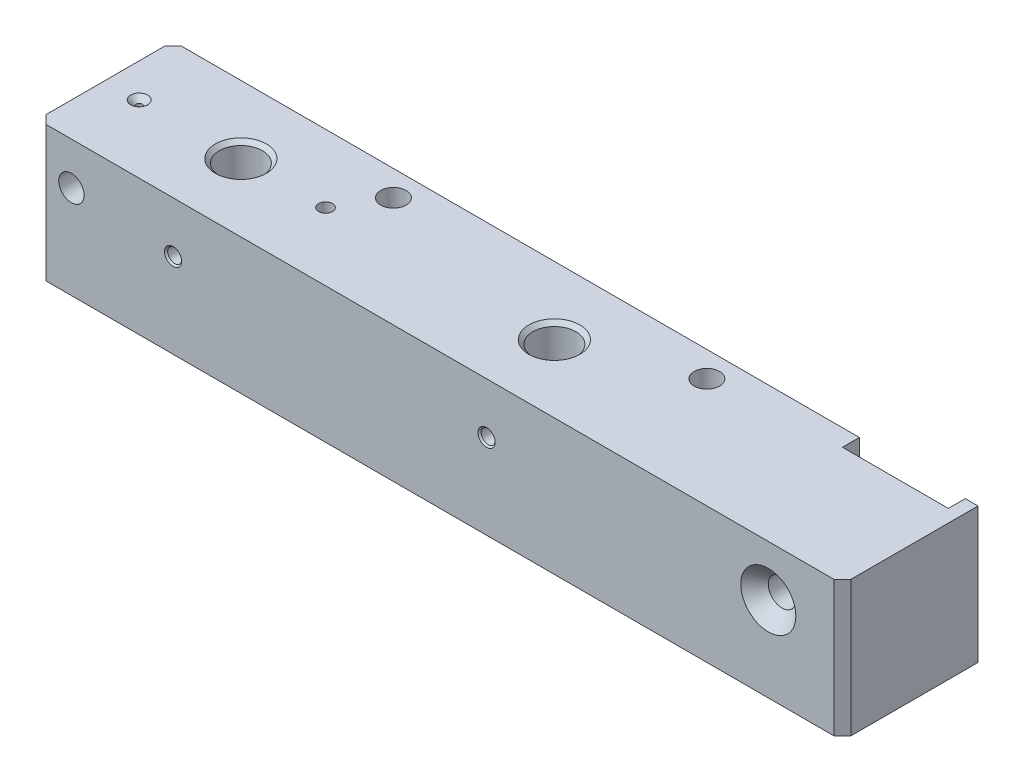
SolidWorks part; units mm, degrees
ref_plane "Front Plane" through (0, 0, 0) normal (0, 0, 1) x (1, 0, 0)
ref_plane "Top Plane" through (0, 0, 0) normal (0, 1, 0) x (1, 0, 0)
ref_plane "Right Plane" through (0, 0, 0) normal (1, 0, 0) x (0, 0, -1)
sketch "Sketch1" plane through (0, 0, 0) normal (0, 0, 1) x (1, 0, 0)
  line L1 (-95, 16) -> (95, 16)
  line L2 (-95, 16) -> (-95, -16)
  line L3 (-95, -16) -> (95, -16)
  line L4 (95, 16) -> (95, -16)
  line L5 (-95, 16) -> (95, -16) construction
  line L6 (-95, -16) -> (95, 16) construction
  point P0 (0, 0)
  dimension "D1" = 190
  dimension "D2" = 32
extrude "Boss-Extrude1" add sketch "Sketch1" along normal mid plane 32
chamfer "Chamfer1" distance 2 angle 45 3 edges at (-95, 0, -16) (-95, 0, 16) (95, 0, 16)
sketch "Sketch2" plane through (0, 16, 0) normal (0, 1, 0) x (1, 0, 0)
  line L0 (95, 16) -> (-93, 16) construction
  line L1 (67, 16) -> (92, 16)
  line L2 (67, 16) -> (67, 12)
  line L3 (67, 12) -> (92, 12)
  line L4 (92, 16) -> (92, 12)
  line L5 (95, -14) -> (95, 16) construction
  dimension "D1" = 25
  dimension "D2" = 4
  dimension "D3" = 3
extrude "Cut-Extrude1" cut sketch "Sketch2" against normal through all
sketch "Sketch3" plane through (0, 16, 0) normal (0, 1, 0) x (1, 0, 0)
  line L0 (-95, 0) -> (95, 0) construction
  line L1 (-95, -14) -> (-95, 14) construction
  line L2 (95, -14) -> (95, 16) construction
  line L3 (-63, 16) -> (-63, -16) construction
  line L4 (67, 16) -> (-93, 16) construction
  line L5 (93, -16) -> (-93, -16) construction
  line L6 (11, 16) -> (11, -16) construction
  line L7 (67, 16) -> (67, 12) construction
  dimension "D1" = 56
  dimension "D2" = 74
hole_wizard "M12 Tapped Hole1" positions "Sketch4" profile "Sketch5" tap size "M12" standard "ISO"
sketch "Sketch4" plane through (0, 16, 0) normal (0, 1, 0) x (1, 0, 0)
  line L0 (-63, 16) -> (-63, -16) construction
  line L1 (11, 16) -> (11, -16) construction
  point P0 (-63, 0)
  point P4 (11, 0)
sketch "Sketch5" plane through (-63, 16, 0) normal (1, 0, 0) x (0, 0, 1)
  line L0 (0, 0) -> (0, 27.0644)
  line L1 (0, 27.0644) -> (5.1, 24)
  line L2 (5.1, 24) -> (5.1, 0.925)
  line L3 (5.1, 0.925) -> (6.025, 0)
  line L5 (6.025, 0) -> (0, 0)
  line L6 (-5.1, 0.925) -> (-6.025, 0) construction
  line L10 (0, 27.0644) -> (-5.1, 24) construction
  line L11 (0, -6.35) -> (0, 107.95) construction
  dimension "Tap Drill Dia." = 10.2
  dimension "Tap Drill Depth" = 24
  dimension "Near C'Sink Dia." = 12.05
  dimension "Near C'Sink Angle" = 90
  dimension "Drill Angle" = 118
cosmetic thread "Hole Thread1" parameters "D1"=24, "D2"=12
cosmetic thread "Hole Thread2" parameters "D1"=24, "D2"=12
sketch "Sketch6" plane through (0, 0, 16) normal (0, 0, 1) x (1, 0, 0)
  line L0 (-63, -8) -> (-63, 16) construction
  line L1 (-57.9, -8) -> (-68.1, -8) construction
  line L2 (-95, 16) -> (95, 16) construction
  line L3 (11, -8) -> (11, 16) construction
  line L4 (16.1, -8) -> (5.9, -8) construction
  line L5 (-63, 4) -> (11, 4) construction
hole_wizard "M4 Tapped Hole1" positions "Sketch7" profile "Sketch8" tap size "M4" standard "ISO"
sketch "Sketch7" plane through (0, 0, 16) normal (0, 0, 1) x (1, 0, 0)
  point P0 (-63, 4)
  point P3 (11, 4)
sketch "Sketch8" plane through (-63, 4, 16) normal (1, 0, 0) x (0, -1, 0)
  line L0 (0, 0) -> (0, 12.4914)
  line L1 (0, 12.4914) -> (1.65, 11.5)
  line L2 (1.65, 11.5) -> (1.65, 0.375)
  line L3 (1.65, 0.375) -> (2.025, 0)
  line L5 (2.025, 0) -> (0, 0)
  line L6 (-1.65, 0.375) -> (-2.025, 0) construction
  line L10 (0, 12.4914) -> (-1.65, 11.5) construction
  line L11 (0, -6.35) -> (0, 107.95) construction
  dimension "Tap Drill Dia." = 3.3
  dimension "Tap Drill Depth" = 11.5
  dimension "Near C'Sink Dia." = 4.05
  dimension "Near C'Sink Angle" = 90
  dimension "Drill Angle" = 118
cosmetic thread "Hole Thread3" parameters "D1"=8, "D2"=4
cosmetic thread "Hole Thread4" parameters "D1"=8, "D2"=4
sketch "Sketch9" plane through (0, 0, 16) normal (0, 0, 1) x (1, 0, 0)
  line L0 (77.5, -16) -> (77.5, 16) construction
  line L1 (-93, -16) -> (93, -16) construction
  line L2 (-95, 16) -> (95, 16) construction
  line L3 (77.5, 4) -> (93, 4) construction
  line L4 (93, -16) -> (93, 16) construction
  dimension "D1" = 20
  dimension "D2" = 15.5
hole_wizard "CSK for M10 Countersunk Flat Head Screw1" positions "Sketch10" profile "Sketch11" countersink size "M10" standard "ISO" end condition through all
sketch "Sketch10" plane through (0, 0, 16) normal (0, 0, 1) x (1, 0, 0)
  point P0 (77.5, 4)
sketch "Sketch11" plane through (77.5, 4, 16) normal (1, 0, 0) x (0, -1, 0)
  line L0 (0, 0) -> (0, 32)
  line L1 (0, 32) -> (3.25, 32)
  line L2 (3.25, 32) -> (3.25, 3.25)
  line L3 (3.25, 3.25) -> (6.5, 0)
  line L5 (6.5, 0) -> (0, 0)
  line L6 (-3.25, 3.25) -> (-6.5, 0) construction
  line L11 (0, -6.35) -> (0, 107.95) construction
  dimension "Thru Hole Dia." = 6.5
  dimension "Thru Hole Depth" = 32
  dimension "Near C'Sink Dia." = 13
  dimension "Near C'Sink Angle" = 90
sketch "Sketch12" plane through (0, 0, 16) normal (0, 0, 1) x (1, 0, 0)
  line L0 (-63, 4) -> (-85.9698, 4) construction
  line L1 (-87, 4) -> (-87, 16) construction
  line L2 (-95, 16) -> (95, 16) construction
  line L3 (-93, -16) -> (93, -16) construction
  circle A0 centre (-87, 6) radius 3
  point P9 (-125.9737, 21.9002)
  point P10 (0, 0)
  dimension "D2" = 6
  dimension "D1" = 24
  dimension "D3" = 22
extrude "Cut-Extrude2" cut sketch "Sketch12" against normal through all
hole_wizard "CSK for M4 Countersunk Flat Head Screw1" positions "Sketch13" profile "Sketch14" countersink size "M4" standard "ISO"
sketch "Sketch13" plane through (0, 16, 0) normal (0, 1, 0) x (1, 0, 0)
  line L0 (-95, 0) -> (95, 0) construction
  point P0 (-87, 0)
  dimension "D1" = 24
sketch "Sketch14" plane through (-87, 16, 0) normal (1, 0, 0) x (0, 0, 1)
  line L0 (0, 0) -> (0, 11.9506)
  line L1 (0, 11.9506) -> (0.75, 11.5)
  line L2 (0.75, 11.5) -> (0.75, 1.25)
  line L3 (0.75, 1.25) -> (2, 0)
  line L5 (2, 0) -> (0, 0)
  line L6 (-0.75, 1.25) -> (-2, 0) construction
  line L10 (0, 11.9506) -> (-0.75, 11.5) construction
  line L11 (0, -6.35) -> (0, 107.95) construction
  dimension "Hole Dia." = 1.5
  dimension "Hole Depth" = 11.5
  dimension "Near C'Sink Dia." = 4
  dimension "Near C'Sink Angle" = 90
  dimension "Drill Angle" = 118
hole_wizard "M4 Tapped Hole2" positions "Sketch17" profile "Sketch18" tap size "M4" standard "ISO"
sketch "Sketch17" plane through (0, 16, 0) normal (0, 1, 0) x (1, 0, 0)
  line L0 (-95, 0) -> (95, 0) construction
  point P0 (-43, 0)
  dimension "D1" = 20
sketch "Sketch18" plane through (-43, 16, 0) normal (1, 0, 0) x (0, 0, 1)
  line L0 (0, 0) -> (0, 16.9914)
  line L1 (0, 16.9914) -> (1.65, 16)
  line L2 (1.65, 16) -> (1.65, 0)
  line L5 (1.65, 0) -> (0, 0)
  line L10 (0, 16.9914) -> (-1.65, 16) construction
  line L11 (0, -6.35) -> (0, 107.95) construction
  dimension "Tap Drill Dia." = 3.3
  dimension "Tap Drill Depth" = 16
  dimension "Drill Angle" = 118
cosmetic thread "Hole Thread5" parameters "D1"=8, "D2"=4
sketch "Sketch19" plane through (0, 16, 0) normal (0, 1, 0) x (1, 0, 0)
  line L0 (-95, -14) -> (-95, 14) construction
  line L1 (67, 16) -> (-93, 16) construction
  circle A0 centre (-37, 10) radius 3
  circle A1 centre (37, 10) radius 3
  point P6 (0, 0)
  point P7 (0, 0)
  point P8 (-36.5158, 13.0692)
  point P9 (-38.0053, 13.618)
  point P12 (0, 0)
  dimension "D3" = 6
  dimension "D4" = 74
  dimension "D1" = 58
  dimension "D2" = 6
extrude "Cut-Extrude3" cut sketch "Sketch19" against normal through all
